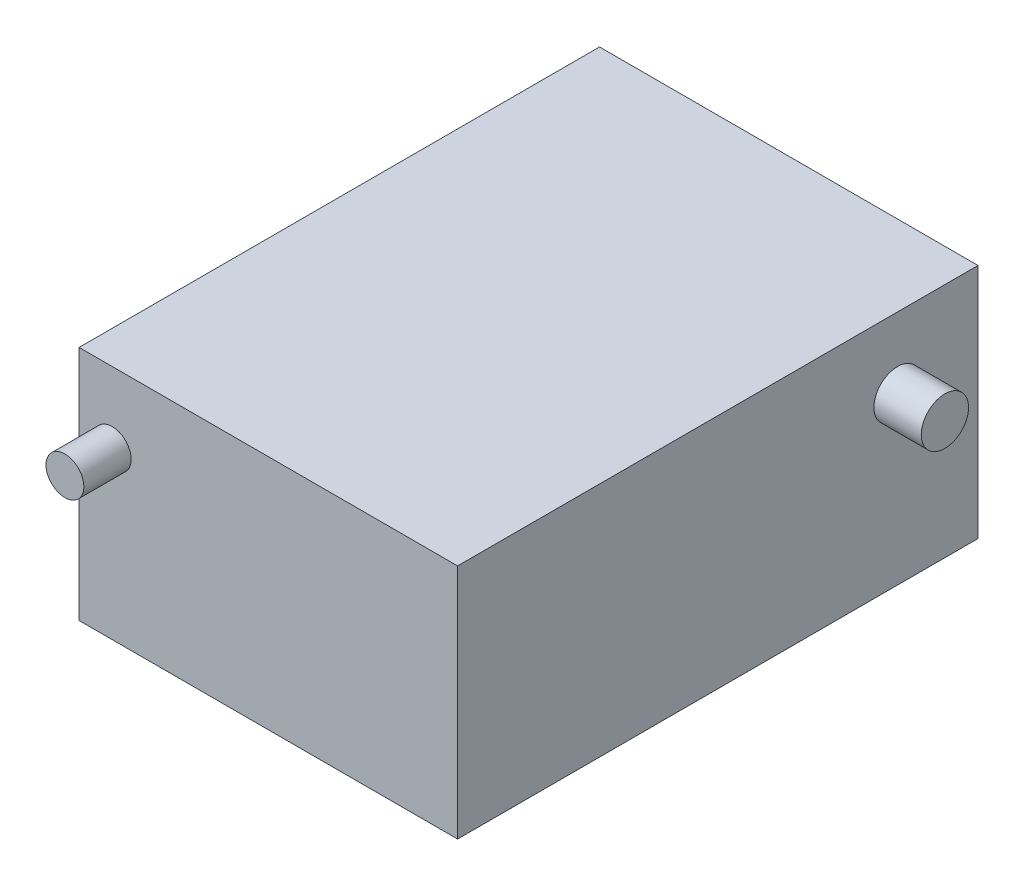
SolidWorks part; units mm, degrees
ref_plane "前视基准面" through (0, 0, 0) normal (0, 0, 1) x (1, 0, 0)
ref_plane "上视基准面" through (0, 0, 0) normal (0, 1, 0) x (1, 0, 0)
ref_plane "右视基准面" through (0, 0, 0) normal (1, 0, 0) x (0, 0, -1)
other "Configuration Table"
sketch "Sketch1" plane through (0, 0, 0) normal (1, 0, 0) x (0, 0, -1)
  line L1 (0, 0) -> (110, 0)
  line L2 (0, 0) -> (0, 50)
  line L3 (0, 50) -> (110, 50)
  line L4 (110, 0) -> (110, 50)
  dimension "D1" = 110
  dimension "D2" = 50
extrude "Boss-Extrude1" add sketch "Sketch1" along normal blind 80
sketch "Sketch2" plane through (0, 0, 0) normal (0, 0, 1) x (1, 0, 0)
  line L1 (0, 50) -> (0, 0) construction
  line L2 (80, 50) -> (0, 50) construction
  circle A0 centre (7, 35) radius 4
  point P6 (5.4111, 6.946)
  dimension "D3" = 8
  dimension "D1" = 15
  dimension "D2" = 7
extrude "Boss-Extrude2" add sketch "Sketch2" along normal blind 10
sketch "Sketch3" plane through (80, 0, 0) normal (1, 0, 0) x (0, 0, -1)
  line L1 (110, 0) -> (110, 50) construction
  line L2 (110, 50) -> (0, 50) construction
  circle A0 centre (93, 35) radius 5
  dimension "D3" = 10
  dimension "D1" = 15
  dimension "D2" = 17
extrude "Boss-Extrude3" add sketch "Sketch3" along normal blind 10
